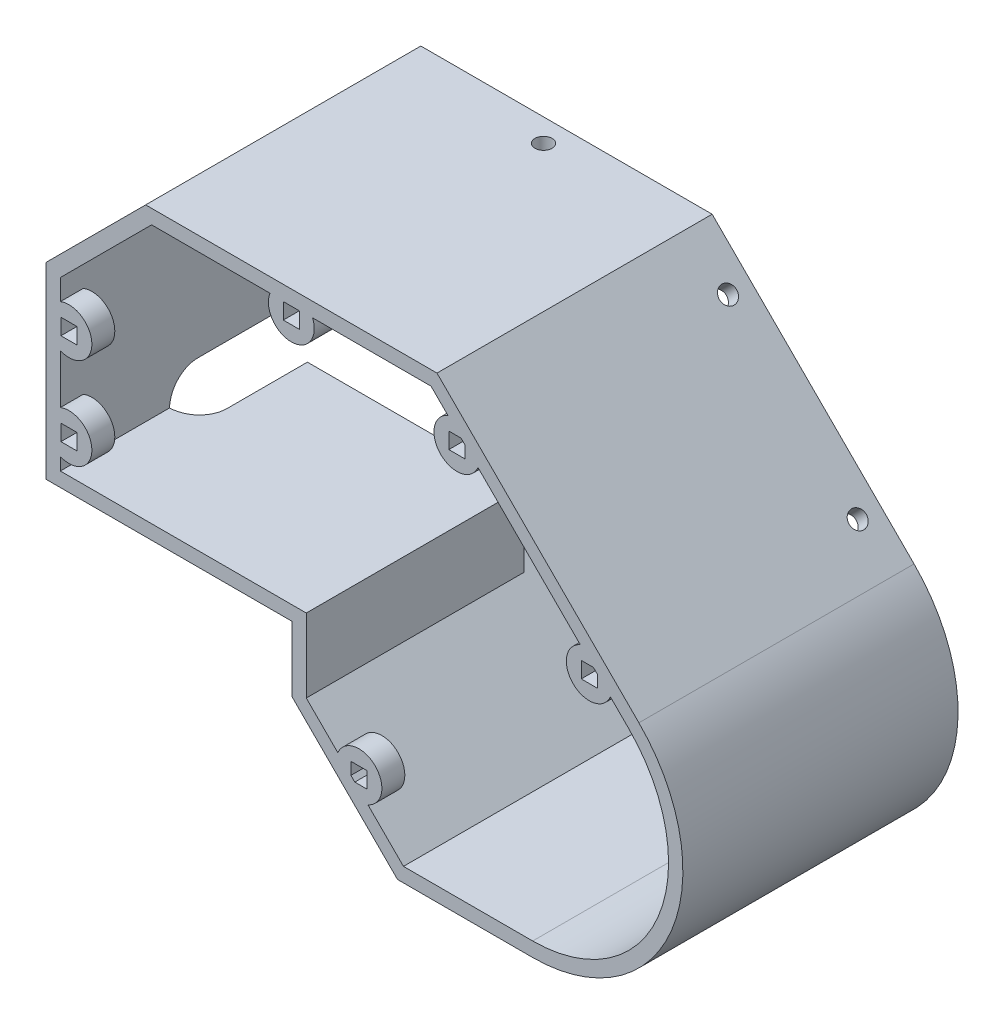
SolidWorks part; units mm, degrees
ref_plane "Plano frontal" through (0, 0, 0) normal (0, 0, 1) x (1, 0, 0)
ref_plane "Plano superior" through (0, 0, 0) normal (0, 1, 0) x (1, 0, 0)
ref_plane "Plano direito" through (0, 0, 0) normal (1, 0, 0) x (0, 0, -1)
sketch "Model" plane through (0, 0, 0) normal (0, 0, 1) x (1, 0, 0)
  line L0 (0, 0) -> (39, 0) construction
  line L1 (-0.7, 2.5) -> (39, 2.5)
  line L2 (39.7, 0) -> (39.7, -6.8548) construction
  line L3 (0, 0) -> (0, 31.4419) construction
  line L4 (50.1111, 46.949) -> (15.5071, 46.949) construction
  line L5 (0, 31.4419) -> (15.5071, 46.949) construction
  line L6 (42.2, -9.3548) -> (52.4452, -19.6) construction
  line L7 (39, -7.1448) -> (51.9502, -20.095) construction
  line L8 (97.9635, 12.6635) -> (63.6779, 46.949) construction
  line L9 (50.1111, 46.949) -> (63.6779, 46.949) construction
  line L10 (52.4452, -19.6) -> (59.4452, -26.6) construction
  line L11 (81.7, -26.6) -> (59.4452, -26.6) construction
  line L12 (-0.7, 0) -> (39, 0)
  line L13 (-0.7, 0) -> (-3.2, 0)
  line L14 (42.2, -10.3448) -> (51.9502, -20.095)
  line L15 (51.9502, -20.095) -> (59.1552, -27.3)
  line L16 (81.7, -27.3) -> (59.1552, -27.3)
  line L17 (98.4584, 13.1584) -> (63.9678, 47.649)
  line L18 (50.1111, 47.649) -> (63.9678, 47.649)
  line L19 (50.1111, 47.649) -> (15.2171, 47.649)
  line L20 (-0.7, 31.7319) -> (15.2171, 47.649)
  line L21 (-0.7, 2.5) -> (-0.7, 31.7319)
  line L22 (0, 0) -> (-0.7, 0) construction
  line L23 (38.8515, -10.5318) -> (50.1824, -21.8627) construction
  line L24 (-3.2, 0) -> (-3.2, 5)
  line L25 (-0.7, -0.7) -> (-0.7, 31.7319) construction
  line L26 (-0.7, -0.7) -> (39, -0.7) construction
  line L27 (39, -0.7) -> (39, -7.1448) construction
  line L28 (39, -0.7) -> (39, -0.7) construction
  line L29 (39, 0) -> (39.7, 0)
  line L30 (39.7, 0) -> (39.7, -11.3803)
  line L31 (39, 2.5) -> (39.7, 2.5)
  line L32 (39.7, 2.5) -> (42.2, 2.5)
  line L33 (39, 0) -> (39.7, 0) construction
  line L34 (42.2, 2.5) -> (42.2, -10.3448)
  line L35 (-3.2, 5) -> (-3.2, 32.7674)
  line L36 (-3.2, 32.7674) -> (14.1816, 50.149)
  line L37 (50.1111, 50.149) -> (14.1816, 50.149)
  line L38 (50.1111, 50.149) -> (65.0034, 50.149)
  line L39 (100.2262, 14.9262) -> (65.0034, 50.149)
  line L40 (81.7, -29.8) -> (58.1197, -29.8)
  line L41 (50.1824, -21.8627) -> (58.1197, -29.8)
  line L42 (39.7, -11.3803) -> (50.1824, -21.8627)
  line L43 (-0.7, 2.5) -> (-5.7, 2.5) construction
  line L44 (-5.7, 0) -> (-5.7, 2.5) construction
  line L45 (-0.7, 0) -> (-5.7, 0) construction
  line L46 (-3.2, 5) -> (-8.2, 5) construction
  line L47 (-8.2, -2.5) -> (-8.2, 5) construction
  line L48 (-0.7, -2.5) -> (39, -2.5) construction
  line L49 (-0.7, -2.5) -> (-8.2, -2.5) construction
  line L51 (40.6192, -8.764) -> (51.9502, -20.095) construction
  line L52 (39.7, -6.8548) -> (52.4452, -19.6) construction
  arc A0 (81.7, -27.3) -> (98.4584, 13.1584) centre (81.7, -3.6) ccw
  arc A1 (81.7, -29.8) -> (100.2262, 14.9262) centre (81.7, -3.6) ccw
  circle A2 centre (59.0726, 19.0274) radius 7.35 construction
  arc A5 (81.7, -26.6) -> (97.9635, 12.6635) centre (81.7, -3.6) ccw construction
  circle A6 centre (81.7, -3.6) radius 7.3 construction
  circle A13 centre (27.384, 23.481) radius 7.35 construction
  dimension "D2" = 2.5
  dimension "D1" = 0.7
extrude "Ressalto-extrusão1" add sketch "Model" along normal blind 48
sketch "Esboço12" plane through (57.5762, 57.5762, 0) normal (0.7071, 0.7071, 0) x (0, 0, -1)
  line L0 (-48, -35.4099) -> (-44, -35.4099) construction
  line L1 (-48, -60.3162) -> (-48, -10.5036) construction
  line L2 (-44, -35.4099) -> (-44, -43.4099) construction
  line L7 (-45.4, -52.0727) -> (-44, -52.0727) construction
  line L9 (-45.4, -20.0727) -> (-44, -20.0727) construction
  circle A0 centre (-44, -20.0727) radius 1.5
  circle A1 centre (-44, -52.0727) radius 1.5
extrude "Corte-extrusão10" cut sketch "Esboço12" against normal blind 10
sketch "Esboço13" plane through (0, 50.149, 0) normal (0, 1, 0) x (1, 0, 0)
  line L0 (39.5925, -48) -> (39.5925, -44) construction
  line L1 (65.0034, -48) -> (14.1816, -48) construction
  circle A0 centre (39.5925, -44) radius 1.5
extrude "Corte-extrusão11" cut sketch "Esboço13" against normal blind 10
sketch "Esboço14" plane through (-3.2, 0, 0) normal (-1, 0, 0) x (0, 0, 1)
  line L0 (48, 16.3837) -> (44, 16.3837) construction
  line L1 (48, 32.7674) -> (48, 0) construction
  line L2 (45.3801, 22.301) -> (45.3801, 25.101) construction
  line L3 (45.3626, 6.3583) -> (45.3626, 9.1235) construction
  line L4 (45.3801, 22.301) -> (45.3801, 25.101) construction
  line L5 (45.3626, 6.3583) -> (45.3626, 9.1235) construction
  line L6 (45.3801, 23.701) -> (44, 23.701) construction
  line L7 (45.3626, 7.7409) -> (44, 7.7409) construction
  circle A0 centre (44, 23.701) radius 1.5
  circle A1 centre (44, 7.7409) radius 1.5
extrude "Corte-extrusão12" cut sketch "Esboço14" against normal blind 10
sketch "Esboço15" plane through (14.1598, 14.1598, 0) normal (-0.7071, -0.7071, 0) x (0, 0, 1)
  line L0 (48, -62.1686) -> (44, -62.1686) construction
  line L1 (48, -62.1686) -> (0, -62.1686) construction
  line L2 (0, -36.4548) -> (0, -50.9436) construction
  line L3 (0, -50.9436) -> (0, -60.8431) construction
  line L4 (0, -36.4548) -> (0, -50.9436) construction
  line L5 (0, -50.9436) -> (0, -60.8431) construction
  line L6 (0, -60.8431) -> (0, -36.4548) construction
  line L7 (0, -36.4548) -> (0, -48.6489) construction
  line L8 (0, -48.6489) -> (48, -48.6489) construction
  line L9 (48, -36.1192) -> (48, -62.1686) construction
  line L11 (45.4, -48.2812) -> (45.4, -45.4812) construction
  line L12 (45.4, -48.2812) -> (45.4, -45.4812) construction
  line L13 (45.4, -46.8812) -> (44, -46.8812) construction
  circle A0 centre (44, -46.8812) radius 1.5
extrude "Corte-extrusão13" cut sketch "Esboço15" against normal blind 10
sketch "Esboço16" plane through (0, 0, 48) normal (0, 0, 1) x (1, 0, 0)
  line L0 (39.7, 0) -> (39.7, -7.8448)
  line L3 (42.2, -10.3448) -> (39.7, -7.8448)
  line L4 (42.2, -10.3448) -> (42.2, 2.5)
  line L5 (42.2, 2.5) -> (-0.7, 2.5)
  line L6 (39.7, 0) -> (39.7, -7.8448) construction
  line L12 (-0.7, 0) -> (39.7, 0)
  line L13 (-0.7, 2.5) -> (-0.7, 0)
extrude "Corte-extrusão14" cut sketch "Esboço16" against normal blind 10
sketch "Esboço17" plane through (0, 0, 0) normal (0, 0, -1) x (-1, 0, 0)
  line L0 (-93.3365, 21.8159) -> (-95.4578, 19.6946) construction
  line L1 (-93.3365, 21.8159) -> (-95.4578, 19.6946) construction
  line L2 (-70.709, 44.4433) -> (-72.8304, 42.322) construction
  line L3 (-70.709, 44.4433) -> (-72.8304, 42.322) construction
  line L4 (-38.0925, 50.149) -> (-41.0925, 50.149) construction
  line L5 (-38.0925, 50.149) -> (-41.0925, 50.149) construction
  line L6 (3.2, 22.201) -> (3.2, 25.201) construction
  line L7 (3.2, 22.201) -> (3.2, 25.201) construction
  line L8 (3.2, 6.2409) -> (3.2, 9.2409) construction
  line L9 (3.2, 6.2409) -> (3.2, 9.2409) construction
  line L10 (-48.3705, -20.0508) -> (-46.2492, -17.9295) construction
  line L11 (-48.3705, -20.0508) -> (-46.2492, -17.9295) construction
  line L12 (-94.3971, 20.7553) -> (-91.5687, 17.9268) construction
  line L14 (-39.5925, 50.149) -> (-39.5925, 46.149) construction
  line L18 (-69.8727, 39.6229) -> (-67.0727, 39.6229)
  line L19 (-92.9687, 19.3268) -> (-90.1687, 19.3268)
  line L20 (-92.9687, 19.3268) -> (-92.9687, 16.5268)
  line L21 (-92.9687, 16.5268) -> (-90.1687, 16.5268)
  line L22 (-90.1687, 19.3268) -> (-90.1687, 16.5268)
  line L23 (-92.9687, 19.3268) -> (-90.1687, 16.5268) construction
  line L24 (-92.9687, 16.5268) -> (-90.1687, 19.3268) construction
  line L25 (-69.8727, 39.6229) -> (-67.0727, 42.4229) construction
  line L26 (-69.8727, 42.4229) -> (-67.0727, 39.6229) construction
  line L27 (-69.8727, 42.4229) -> (-69.8727, 39.6229)
  line L28 (-69.8727, 42.4229) -> (-67.0727, 42.4229)
  line L29 (-67.0727, 42.4229) -> (-67.0727, 39.6229)
  line L30 (-38.1925, 47.549) -> (-38.1925, 44.749)
  line L31 (-40.9925, 44.749) -> (-38.1925, 47.549) construction
  line L32 (-40.9925, 47.549) -> (-40.9925, 44.749)
  line L33 (-40.9925, 47.549) -> (-38.1925, 44.749) construction
  line L34 (-40.9925, 44.749) -> (-38.1925, 44.749)
  line L35 (-40.9925, 47.549) -> (-38.1925, 47.549)
  line L36 (-2.2, 25.7837) -> (0.6, 22.9837) construction
  line L37 (-2.2, 22.9837) -> (0.6, 22.9837)
  line L38 (0.6, 25.7837) -> (0.6, 22.9837)
  line L39 (-2.2, 25.7837) -> (0.6, 25.7837)
  line L40 (-2.2, 22.9837) -> (0.6, 25.7837) construction
  line L41 (-2.2, 25.7837) -> (-2.2, 22.9837)
  line L42 (0.6, 9.7837) -> (0.6, 6.9837)
  line L43 (-2.2, 9.7837) -> (0.6, 9.7837)
  line L44 (-2.2, 6.9837) -> (0.6, 6.9837)
  line L45 (-2.2, 9.7837) -> (0.6, 6.9837) construction
  line L46 (-2.2, 9.7837) -> (-2.2, 6.9837)
  line L47 (-2.2, 6.9837) -> (0.6, 9.7837) construction
  line L48 (-52.7883, -18.8117) -> (-49.9883, -18.8117)
  line L49 (-52.7883, -16.0117) -> (-49.9883, -18.8117) construction
  line L50 (-52.7883, -18.8117) -> (-49.9883, -16.0117) construction
  line L51 (-52.7883, -16.0117) -> (-49.9883, -16.0117)
  line L52 (-49.9883, -16.0117) -> (-49.9883, -18.8117)
  line L53 (-52.7883, -16.0117) -> (-52.7883, -18.8117)
  circle A0 centre (-91.5687, 17.9268) radius 4
  circle A1 centre (-68.4727, 41.0229) radius 4
  circle A2 centre (-39.5925, 46.149) radius 4
  circle A3 centre (-0.8, 24.3837) radius 4
  circle A4 centre (-0.8, 8.3837) radius 4
  circle A5 centre (-51.3883, -17.4117) radius 4
extrude "Ressalto-extrusão2" add sketch "Esboço17" against normal blind 4
sketch "Esboço18" plane through (0, 0, 48) normal (0, 0, 1) x (1, 0, 0)
  line L0 (-0.7, 31.7319) -> (-32.4319, 0)
  line L1 (15.2171, 47.649) -> (-0.7, 31.7319) construction
  line L2 (-0.7, 31.7319) -> (-0.7, 0)
  line L3 (-0.7, 0) -> (-32.4319, 0)
extrude "Corte-extrusão15" cut sketch "Esboço18" against normal up to surface (10 mm away) up to face at (27.0667, -2.1983, 38)
sketch "Esboço19" plane through (-3.2, 0, 0) normal (-1, 0, 0) x (0, 0, 1)
  line L0 (48, -11.3803) -> (0, -11.3803) construction
  line L1 (48, -11.3803) -> (0, -11.3803) construction
  line L2 (24, -11.3803) -> (24, 0) construction
  line L3 (38, 0) -> (0, 0) construction
  line L4 (19, 0) -> (29, 0)
  line L5 (19, 0) -> (19, 3)
  line L7 (19, 3) -> (29, 3) construction
  line L8 (24, 8) -> (38.2569, 8)
  line L9 (38.2569, 8) -> (38.2569, 0)
  line L10 (38.2569, 0) -> (29, 0)
  arc A0 (24, 8) -> (19, 3) centre (24, 3) ccw
revolve "Corte-Revolução1" cut sketch "Esboço19" angle 360 about L4
mirror "Espelhar1" about plane through (81.7, -3.6, 48) normal (0, 0, 1) of bodies 118
sketch "Esboço20" plane through (0, 0, 0) normal (0, 0, -1) x (-1, 0, 0)
  circle A0 centre (-60.2658, 14.046) radius 86.4094
extrude "Corte-extrusão16" cut sketch "Esboço20" against normal up to vertex (48 mm away)
